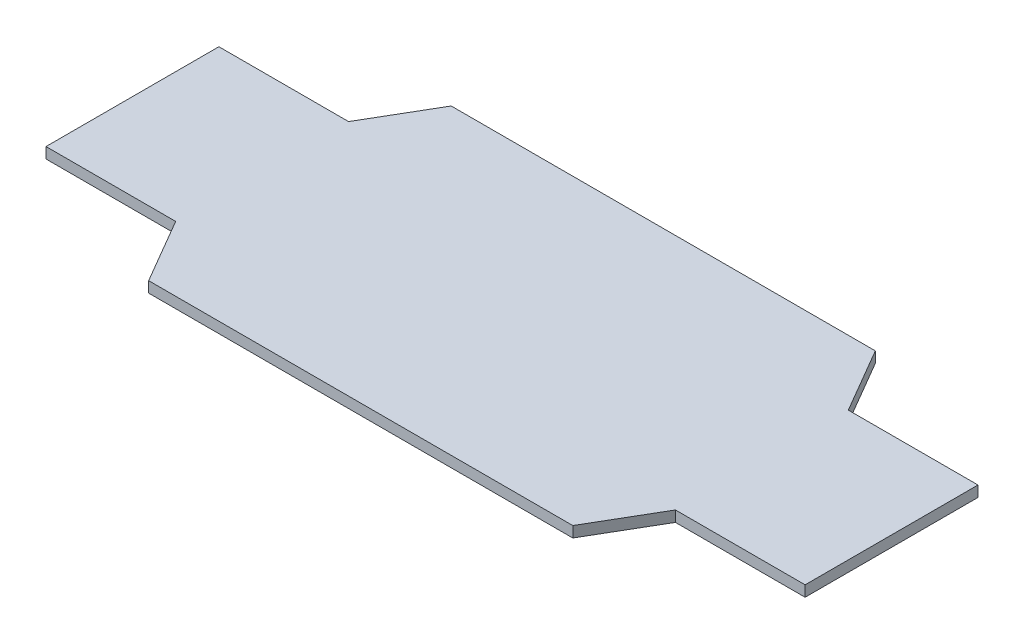
SolidWorks part; units mm, degrees
ref_plane "Front Plane" through (0, 0, 0) normal (0, 0, 1) x (1, 0, 0)
ref_plane "Top Plane" through (0, 0, 0) normal (0, 1, 0) x (1, 0, 0)
ref_plane "Right Plane" through (0, 0, 0) normal (1, 0, 0) x (0, 0, -1)
sketch "Sketch1" plane through (0, 0, 0) normal (0, 1, 0) x (1, 0, 0)
  line L9 (178.435, 40.64) -> (117.475, 40.64)
  line L29 (0, 0) -> (0, 71.12) construction
  line L30 (-178.435, 0) -> (178.435, 0) construction
  line L31 (117.475, 40.64) -> (99.695, 71.12)
  line L32 (99.695, 71.12) -> (-99.695, 71.12)
  line L33 (-99.695, 71.12) -> (-117.475, 40.64)
  line L34 (-117.475, 40.64) -> (-178.435, 40.64)
  line L35 (-178.435, 40.64) -> (-178.435, -40.64)
  line L36 (-178.435, -40.64) -> (-117.475, -40.64)
  line L37 (-117.475, -40.64) -> (-99.695, -71.12)
  line L38 (-99.695, -71.12) -> (99.695, -71.12)
  line L39 (99.695, -71.12) -> (117.475, -40.64)
  line L40 (117.475, -40.64) -> (178.435, -40.64)
  line L41 (178.435, -40.64) -> (178.435, 40.64)
  point P0 (0, 0)
  point P9 (0, 0)
  dimension "D1" = 81.28
  dimension "D2" = 71.12
  dimension "D4" = 71.12
  dimension "D5" = 60.96
  dimension "D6" = 199.39
  dimension "D7" = 199.39
  dimension "D8" = 17.78
extrude "Boss-Extrude1" add sketch "Sketch1" along normal blind 5.08
